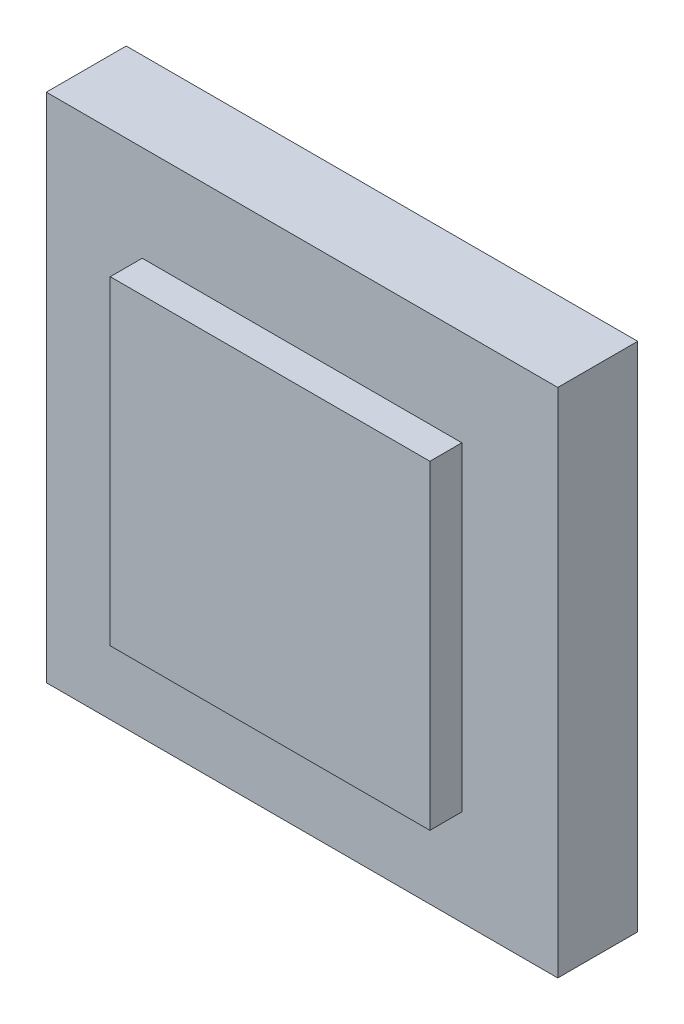
SolidWorks part; units mm, degrees
ref_plane "Front Plane" through (0, 0, 0) normal (0, 0, 1) x (1, 0, 0)
ref_plane "Top Plane" through (0, 0, 0) normal (0, 1, 0) x (1, 0, 0)
ref_plane "Right Plane" through (0, 0, 0) normal (1, 0, 0) x (0, 0, -1)
sketch "Sketch1" plane through (0, 0, 0) normal (0, 0, 1) x (1, 0, 0)
  line L1 (203.2, -203.2) -> (-203.2, -203.2)
  line L2 (203.2, -203.2) -> (203.2, 203.2)
  line L3 (203.2, 203.2) -> (-203.2, 203.2)
  line L4 (-203.2, -203.2) -> (-203.2, 203.2)
  line L5 (203.2, -203.2) -> (-203.2, 203.2) construction
  line L6 (203.2, 203.2) -> (-203.2, -203.2) construction
  point P0 (0, 0)
  dimension "D1" = 406.4
extrude "Boss-Extrude1" add sketch "Sketch1" along normal blind 63.5 contours L4 L3 L2 L1
sketch "Sketch2" plane through (0, 0, 63.5) normal (0, 0, 1) x (1, 0, 0)
  line L1 (127, -127) -> (-127, -127)
  line L2 (127, -127) -> (127, 127)
  line L3 (127, 127) -> (-127, 127)
  line L4 (-127, -127) -> (-127, 127)
  line L5 (127, -127) -> (-127, 127) construction
  line L6 (127, 127) -> (-127, -127) construction
  point P0 (0, 0)
  dimension "D1" = 254
extrude "Boss-Extrude2" add sketch "Sketch2" along normal blind 25.4
